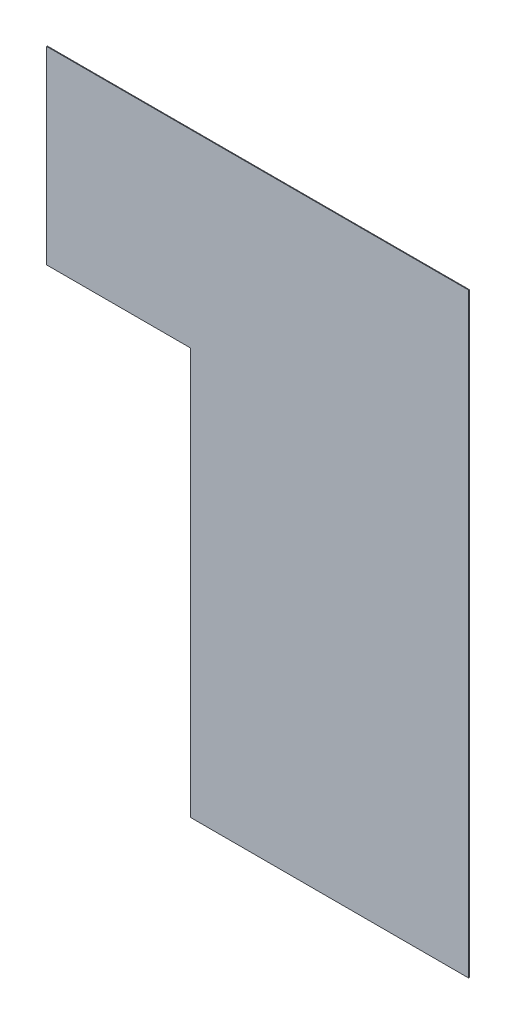
SolidWorks part; units mm, degrees
ref_plane "Plano frontal" through (0, 0, 0) normal (0, 0, 1) x (1, 0, 0)
ref_plane "Plano superior" through (0, 0, 0) normal (0, 1, 0) x (1, 0, 0)
ref_plane "Plano direito" through (0, 0, 0) normal (1, 0, 0) x (0, 0, -1)
sketch "Sketch1" plane through (0, 0, 42225.2208) normal (0, 0, 1) x (1, 0, 0)
  line L1 (-7996.6177, 19917.4814) -> (-19546.6177, 19917.4814)
  line L2 (-7996.6177, 19917.4814) -> (-7996.6177, 14737.0774)
  line L3 (-7996.6177, 14737.0774) -> (-19546.6177, 14737.0774)
  line L4 (-19546.6177, 19917.4814) -> (-19546.6177, 14737.0774)
  line L5 (-7996.6177, 14737.0774) -> (-15606.6177, 14737.0774)
  line L6 (-7996.6177, 14737.0774) -> (-7996.6177, 3607.4814)
  line L7 (-7996.6177, 3607.4814) -> (-15606.6177, 3607.4814)
  line L8 (-15606.6177, 14737.0774) -> (-15606.6177, 3607.4814)
  point P4 (0, 0)
  point P6 (0, 0)
extrude "Boss-Extrude1" add sketch "Sketch1" along normal blind 20 contours L5 L8 L7 L6 | L2 L1 L4 L3
